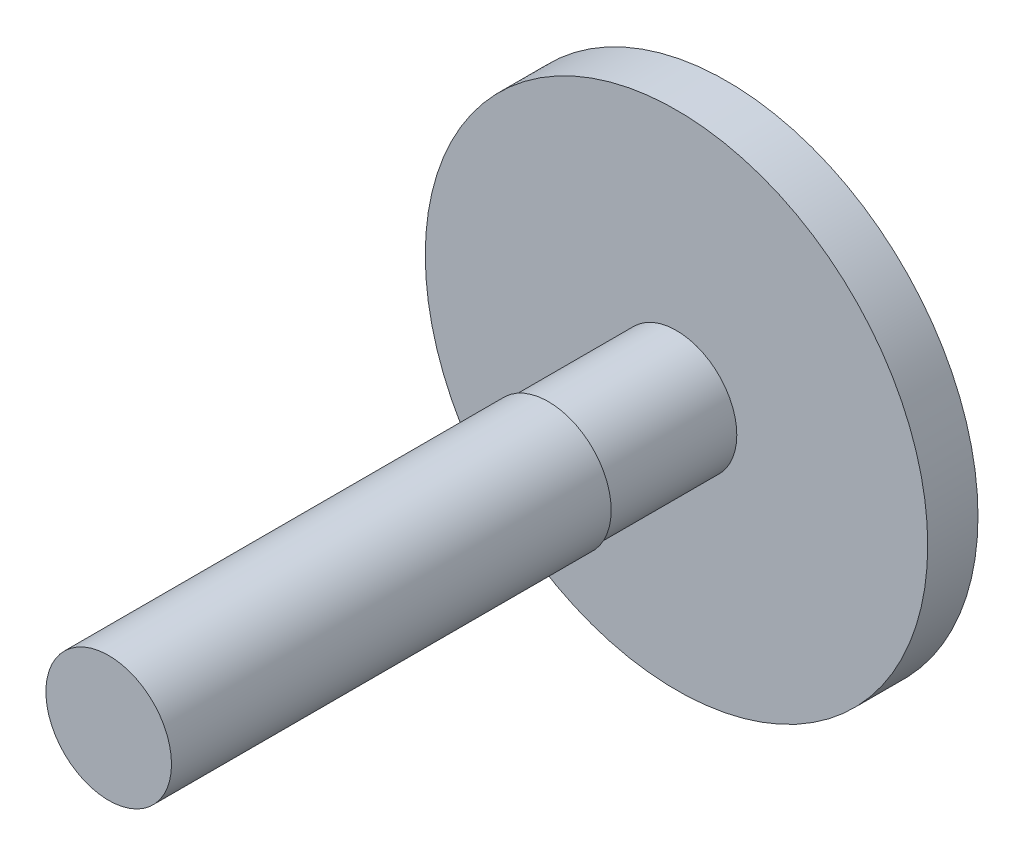
SolidWorks part; units mm, degrees
ref_plane "Front Plane" through (0, 0, 0) normal (0, 0, 1) x (1, 0, 0)
ref_plane "Top Plane" through (0, 0, 0) normal (0, 1, 0) x (1, 0, 0)
ref_plane "Right Plane" through (0, 0, 0) normal (1, 0, 0) x (0, 0, -1)
sketch "Sketch1" plane through (0, 0, 0) normal (0, 0, 1) x (1, 0, 0)
  circle A0 centre (0, 0) radius 10
extrude "Extrude1" add sketch "Sketch1" along normal blind 2
sketch "Sketch2" plane through (0, 0, 2) normal (0, 0, 1) x (1, 0, 0)
  circle A0 centre (0, 0) radius 2.4
extrude "Extrude2" add sketch "Sketch2" along normal blind 5.1
sketch "Sketch3" plane through (0, 0, 7.1) normal (0, 0, 1) x (1, 0, 0)
  circle A0 centre (0, 0) radius 2.5
extrude "Extrude3" add sketch "Sketch3" along normal blind 17.5
